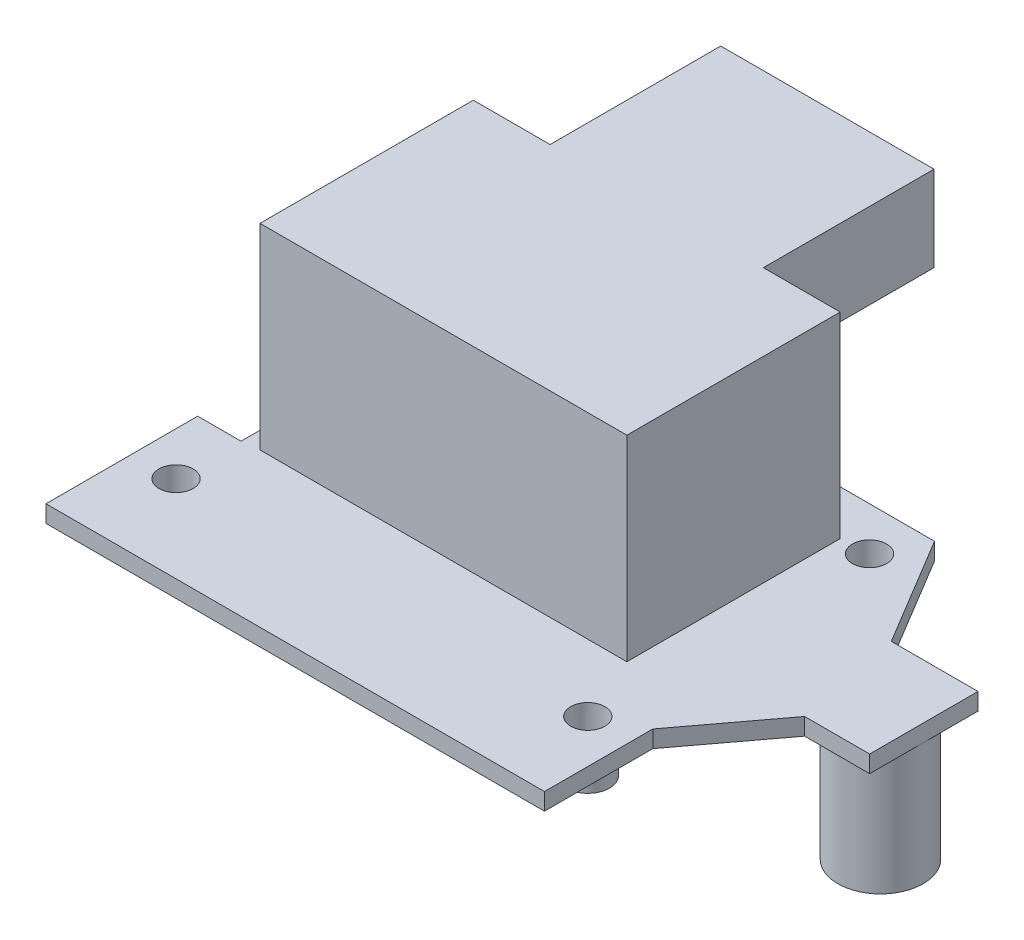
SolidWorks part; units mm, degrees
ref_plane "Front Plane" through (0, 0, 0) normal (0, 0, 1) x (1, 0, 0)
ref_plane "Top Plane" through (0, 0, 0) normal (0, 1, 0) x (1, 0, 0)
ref_plane "Right Plane" through (0, 0, 0) normal (1, 0, 0) x (0, 0, -1)
sketch "Sketch1" plane through (0, 0, 0) normal (0, 1, 0) x (1, 0, 0)
  line L0 (55.88, 48.26) -> (63.5077, 35.5654)
  line L1 (0, 0) -> (58.42, 0)
  line L2 (0, 0) -> (0, 17.78)
  line L3 (5.08, 48.26) -> (55.88, 48.26)
  line L7 (0, 17.78) -> (5.08, 17.78)
  line L8 (5.08, 48.26) -> (5.08, 17.78)
  line L9 (58.42, 12.7) -> (66.0477, 22.8654)
  line L10 (63.5077, 35.5654) -> (73.6677, 35.5654)
  line L12 (66.0477, 22.8654) -> (73.6677, 22.8654)
  line L13 (73.6677, 35.5654) -> (73.6677, 22.8654)
  line L14 (58.42, 0) -> (58.42, 12.7)
  circle A0 centre (5.08, 10.16) radius 2
  circle A1 centre (53.34, 10.16) radius 2
  circle A2 centre (53.34, 43.18) radius 2
  dimension "D14" = 4
  dimension "D17" = 4
  dimension "D18" = 4
  dimension "D1" = 17.78
  dimension "D2" = 5.08
  dimension "D3" = 30.48
  dimension "D4" = 50.8
  dimension "D5" = 58.42
  dimension "D6" = 14.81
  dimension "D7" = 10.16
  dimension "D8" = 7.62
  dimension "D9" = 10.16
  dimension "D10" = 12.7
  dimension "D11" = 12.7
  dimension "D12" = 239
  dimension "D13" = 5.08
  dimension "D15" = 0
  dimension "D16" = 0
  dimension "D19" = 48.26
  dimension "D20" = 33.02
extrude "Boss-Extrude1" add sketch "Sketch1" along normal blind 2
sketch "Sketch2" plane through (0, 2, 0) normal (0, 1, 0) x (1, 0, 0)
  line L0 (5.08, 48.26) -> (5.08, 17.78) construction
  line L1 (7.08, 43) -> (50.08, 43)
  line L2 (7.08, 43) -> (7.08, 18)
  line L3 (7.08, 18) -> (50.08, 18)
  line L4 (50.08, 43) -> (50.08, 18)
  line L5 (0, 0) -> (58.42, 0) construction
  dimension "D1" = 25
  dimension "D2" = 43
  dimension "D3" = 2
  dimension "D4" = 18
extrude "Boss-Extrude2" add sketch "Sketch2" along normal blind 23 contours L1 L4 L3 L2
sketch "Sketch4" plane through (0, 0, 0) normal (0, -1, 0) x (1, 0, 0)
  line L0 (73.6677, -22.8654) -> (73.6677, -35.5654) construction
  line L1 (73.6677, -35.5654) -> (63.5077, -35.5654) construction
  circle A0 centre (68.5877, -29.2154) radius 5
  dimension "D1" = 10
  dimension "D2" = 5.08
  dimension "D3" = 6.35
extrude "Boss-Extrude3" add sketch "Sketch4" along normal blind 14.39
sketch "Sketch5" plane through (0, 0, 0) normal (0, -1, 0) x (1, 0, 0)
  circle A0 centre (5.08, -10.16) radius 2.555
  circle A1 centre (53.34, -10.16) radius 2.555
  circle A2 centre (53.34, -43.18) radius 2.555
  circle A3 centre (53.34, -43.18) radius 2 construction
  circle A4 centre (53.34, -10.16) radius 2 construction
  circle A5 centre (5.08, -10.16) radius 2 construction
  circle A6 centre (53.34, -43.18) radius 2
  circle A7 centre (53.34, -10.16) radius 2
  circle A8 centre (5.08, -10.16) radius 2
  dimension "D1" = 5.11
  dimension "D2" = 5.11
  dimension "D3" = 5.11
extrude "Boss-Extrude4" add sketch "Sketch5" along normal blind 4
sketch "Sketch6" plane through (0, 0, -43) normal (0, 0, -1) x (-1, 0, 0)
  line L0 (-7.08, 2) -> (-50.08, 2) construction
  line L1 (-16.08, 25) -> (-41.08, 25)
  line L2 (-16.08, 25) -> (-16.08, 15)
  line L3 (-16.08, 15) -> (-41.08, 15)
  line L4 (-41.08, 25) -> (-41.08, 15)
  line L5 (-7.08, 25) -> (-7.08, 2) construction
  dimension "D1" = 13
  dimension "D2" = 25
  dimension "D3" = 9
  dimension "D4" = 10
extrude "Boss-Extrude5" add sketch "Sketch6" along normal blind 20
equation "\"D2@Sketch5\"=\"D1@Sketch5\""
equation "\"D3@Sketch5\"=\"D1@Sketch5\""
